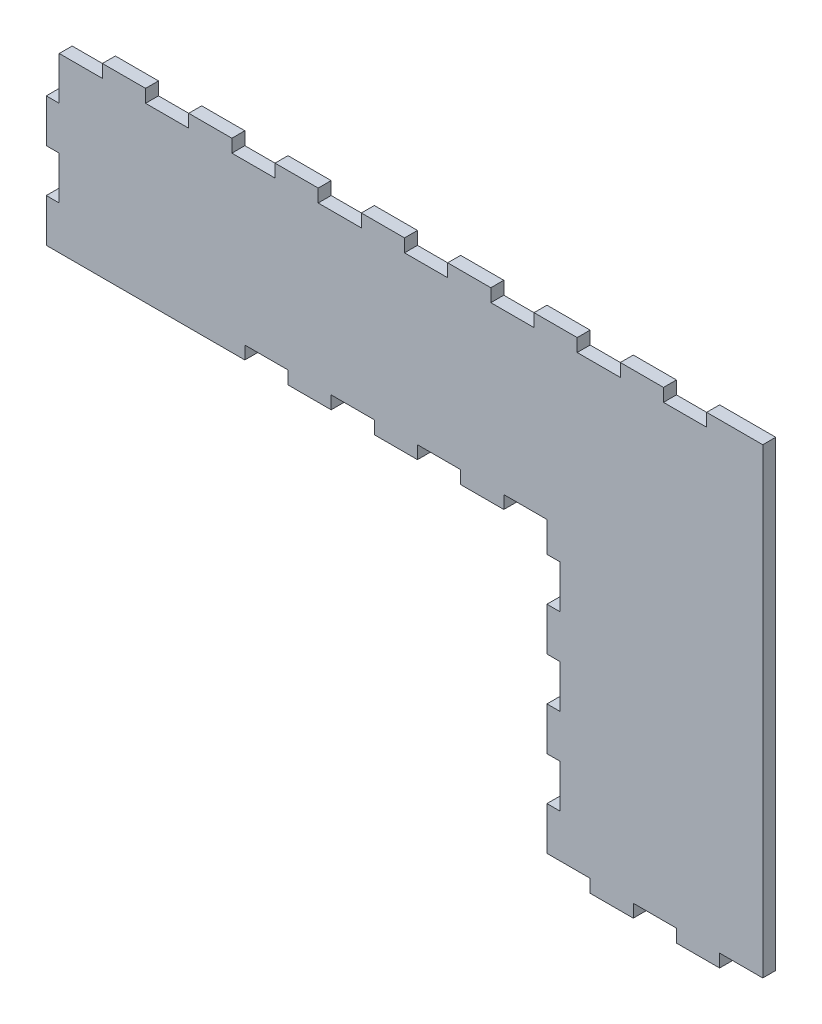
SolidWorks part; units mm, degrees
ref_plane "Plan de face" through (0, 0, 0) normal (0, 0, 1) x (1, 0, 0)
ref_plane "Plan de dessus" through (0, 0, 0) normal (0, 1, 0) x (1, 0, 0)
ref_plane "Plan de droite" through (0, 0, 0) normal (1, 0, 0) x (0, 0, -1)
sketch "Esquisse1" plane through (0, 0, 0) normal (0, 0, 1) x (1, 0, 0)
  line L0 (163, 0) -> (163, -110)
  line L1 (0, 0) -> (163, 0)
  line L2 (0, 0) -> (0, -43)
  line L3 (0, -43) -> (113, -43)
  line L7 (163, -110) -> (113, -110)
  line L8 (113, -43) -> (113, -110)
  dimension "D1" = 163
  dimension "D2" = 43
  dimension "D3" = 110
  dimension "D4" = 50
extrude "Boss.-Extru.1" add sketch "Esquisse1" along normal blind 3 contours L1 L0 L7 L8 L3 L2
sketch "Esquisse2" plane through (0, 0, 3) normal (0, 0, 1) x (1, 0, 0)
  line L1 (0, 0) -> (10, 0)
  line L2 (0, 0) -> (0, -3)
  line L3 (0, -3) -> (10, -3)
  line L4 (10, 0) -> (10, -3)
  dimension "D1" = 10
  dimension "D2" = 3
extrude "Enlèv. mat.-Extru.1" cut sketch "Esquisse2" against normal up to next (3 mm away)
pattern_linear "Répétition linéaire1" count 8 spacing 20 along (1, 0, 0) of "Enlèv. mat.-Extru.1"
sketch "Esquisse4" plane through (0, 0, 0) normal (-1, 0, 0) x (0, 0, 1)
  line L0 (3, -3) -> (3, -43) construction
  line L1 (0, -43) -> (3, -43)
  line L2 (0, -43) -> (0, -33)
  line L3 (0, -33) -> (3, -33)
  line L4 (3, -43) -> (3, -33)
  dimension "D1" = 10
extrude "Boss.-Extru.2" add sketch "Esquisse4" along normal blind 3
pattern_linear "Répétition linéaire3" count 2 spacing 20 along (0, 1, 0) of "Boss.-Extru.2"
sketch "Esquisse5" plane through (0, 0, 3) normal (0, 0, 1) x (1, 0, 0)
  line L1 (113, -43) -> (103, -43)
  line L2 (113, -43) -> (113, -40)
  line L3 (113, -40) -> (103, -40)
  line L4 (103, -43) -> (103, -40)
  dimension "D1" = 10
  dimension "D2" = 3
extrude "Enlèv. mat.-Extru.3" cut sketch "Esquisse5" against normal blind 3
pattern_linear "Répétition linéaire4" count 4 spacing 20 along (-1, 0, 0) of "Enlèv. mat.-Extru.3"
sketch "Esquisse6" plane through (0, 0, 3) normal (0, 0, 1) x (1, 0, 0)
  line L1 (113, -110) -> (123, -110)
  line L2 (113, -110) -> (113, -107)
  line L3 (113, -107) -> (123, -107)
  line L4 (123, -110) -> (123, -107)
  dimension "D1" = 10
  dimension "D2" = 3
extrude "Enlèv. mat.-Extru.4" cut sketch "Esquisse6" against normal blind 3
pattern_linear "Répétition linéaire5" count 3 spacing 20 along (1, 0, 0) of "Enlèv. mat.-Extru.4"
sketch "Esquisse7" plane through (0, 0, 3) normal (0, 0, 1) x (1, 0, 0)
  line L0 (113, -40) -> (113, -107) construction
  line L1 (113, -97) -> (116, -97)
  line L2 (113, -97) -> (113, -87)
  line L3 (113, -87) -> (116, -87)
  line L4 (116, -97) -> (116, -87)
  line L5 (123, -107) -> (113, -107) construction
  dimension "D1" = 10
  dimension "D2" = 10
  dimension "D3" = 3
extrude "Enlèv. mat.-Extru.5" cut sketch "Esquisse7" against normal blind 3
pattern_linear "Répétition linéaire6" count 3 spacing 20 along (0, 1, 0) of "Enlèv. mat.-Extru.5"
